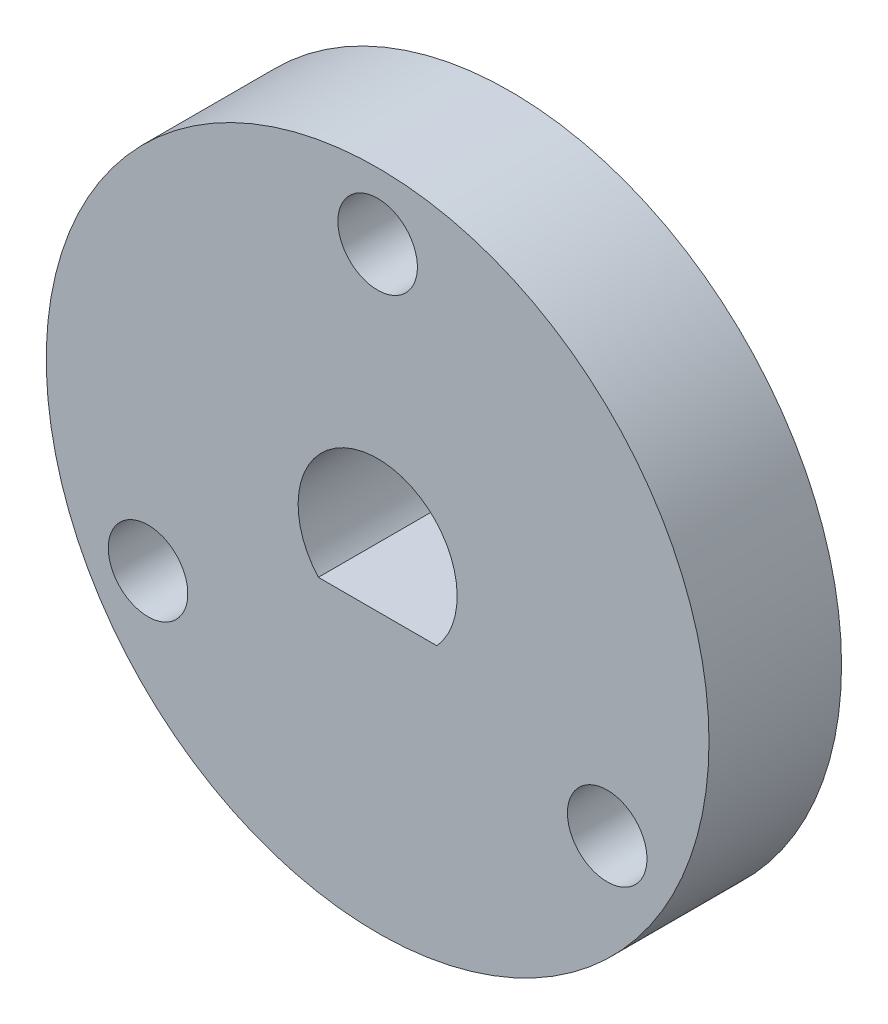
SolidWorks part; units mm, degrees
ref_plane "Front Plane" through (0, 0, 0) normal (0, 0, 1) x (1, 0, 0)
ref_plane "Top Plane" through (0, 0, 0) normal (0, 1, 0) x (1, 0, 0)
ref_plane "Right Plane" through (0, 0, 0) normal (1, 0, 0) x (0, 0, -1)
sketch "Sketch1" plane through (0, 0, 0) normal (0, 0, 1) x (1, 0, 0)
  line L0 (-4.4721, -4) -> (4.4721, -4)
  arc A0 (4.4721, -4) -> (-4.4721, -4) centre (0, 0) ccw
  circle A1 centre (0, 0) radius 25
  point P0 (0, 0)
  dimension "D1" = 50
extrude "Boss-Extrude1" add sketch "Sketch1" against normal blind 10
sketch "Sketch2" plane through (0, 0, -10) normal (0, 0, -1) x (-1, 0, 0)
  circle A0 centre (0, 20) radius 3
  circle A1 centre (17.3205, -10) radius 3
  circle A2 centre (-17.3205, -10) radius 3
  dimension "D2" = 6
  dimension "D1" = 20
  dimension "D3" = 3
extrude "Cut-Extrude1" cut sketch "Sketch2" against normal through all
